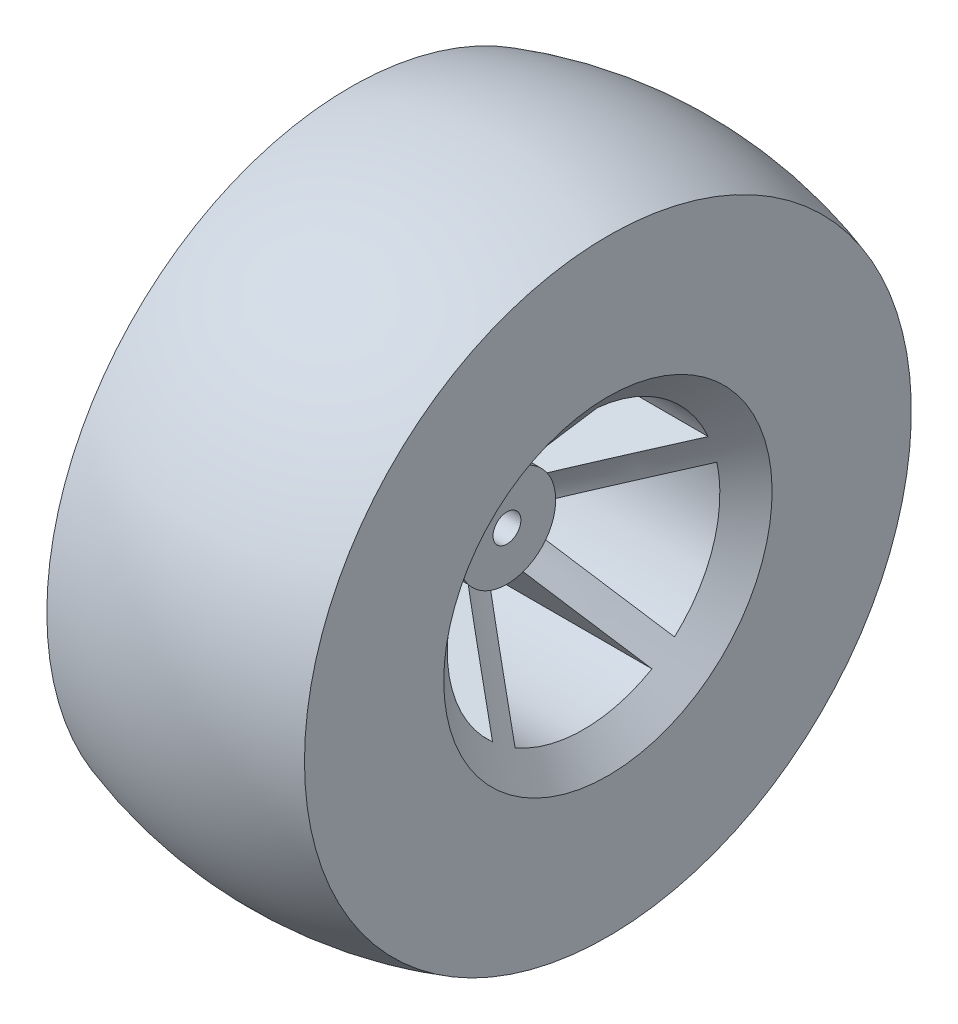
SolidWorks part; units mm, degrees
ref_plane "Front Plane" through (0, 0, 0) normal (0, 0, 1) x (1, 0, 0)
ref_plane "Top Plane" through (0, 0, 0) normal (0, 1, 0) x (1, 0, 0)
ref_plane "Right Plane" through (0, 0, 0) normal (1, 0, 0) x (0, 0, -1)
sketch "Sketch1" plane through (0, 0, 0) normal (0, 1, 0) x (1, 0, 0)
  line L0 (0, -46.5) -> (-98.1265, -46.5) construction
  line L1 (18.5, -43.5767) -> (18.5, -23.5767)
  line L2 (18.5, -23.5767) -> (4, -7)
  line L3 (4, -7) -> (4, -2)
  line L5 (0, -2) -> (0, -46.5)
  line L6 (4, -2) -> (0, -2)
  line L7 (-21.5213, 0) -> (29.4065, 0) construction
  arc A0 (18.5, -43.5767) -> (0, -46.5) centre (0, 13.5) cw
  dimension "D4" = 60
  dimension "D1" = 18.5
  dimension "D2" = 20
  dimension "D3" = 46.5
  dimension "D5" = 5
  dimension "D6" = 4
  dimension "D7" = 2
revolve "Revolve1" add sketch "Sketch1" angle 360 about L7
mirror "Mirror1" about plane through (0, 0, 2) normal (-1, 0, 0) of bodies 101
sketch "Sketch2" plane through (0, 0, 0) normal (1, 0, 0) x (0, 0, -1)
  line L0 (0, 0) -> (0, 19.5767)
  line L1 (0, 0) -> (18.6186, 6.0495)
  line L2 (0, 0) -> (11.5069, -15.8379)
  line L3 (0, 0) -> (-11.5069, -15.8379)
  line L4 (0, 0) -> (-18.6186, 6.0495)
  line L5 (2, 19.4743) -> (2, 2.7528)
  line L6 (2, 2.7528) -> (17.9031, 7.92)
  line L7 (-2, 19.4743) -> (-2, 2.7528)
  line L8 (-2, 2.7528) -> (-17.9031, 7.92)
  line L9 (-19.1392, 4.1158) -> (-3.2361, -1.0515)
  line L10 (-3.2361, -1.0515) -> (-13.0647, -14.5794)
  line L11 (-9.8287, -16.9306) -> (0, -3.4026)
  line L12 (0, -3.4026) -> (9.8287, -16.9306)
  line L13 (13.0647, -14.5794) -> (3.2361, -1.0515)
  line L14 (3.2361, -1.0515) -> (19.1392, 4.1158)
  circle A0 centre (0, 0) radius 19.5767
  circle A1 centre (0, 0) radius 7
  circle A2 centre (0, 0) radius 7 construction
  circle A3 centre (0, 0) radius 23.5767 construction
  dimension "D1" = 4
  dimension "D2" = 72
  dimension "D3" = 72
  dimension "D4" = 72
  dimension "D5" = 72
  dimension "D6" = 4
extrude "Cut-Extrude1" cut sketch "Sketch2" against normal through all both and the other way through all contours A1 L7 A0 L8 | A1 L6 A0 L5 | A1 L9 A0 L10 | A1 L13 A0 L14 | A1 L11 A0 L12
